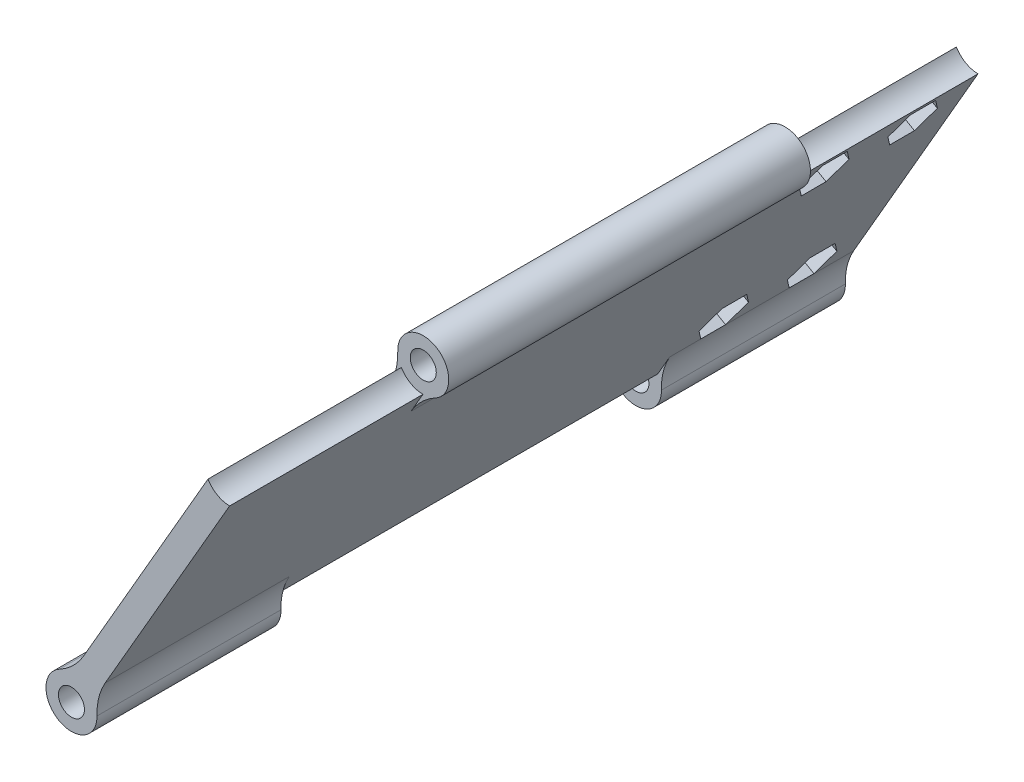
SolidWorks part; units mm, degrees
ref_plane "Front Plane" through (0, 0, 0) normal (0, 0, 1) x (1, 0, 0)
ref_plane "Top Plane" through (0, 0, 0) normal (0, 1, 0) x (1, 0, 0)
ref_plane "Right Plane" through (0, 0, 0) normal (1, 0, 0) x (0, 0, -1)
sketch "Sketch2" plane through (0, 0, 0) normal (0, 0, 1) x (1, 0, 0)
  line L0 (0, 0) -> (38.1, 0)
  line L1 (0, 0) -> (0, -38.1)
  circle A0 centre (0, 0) radius 38.1
  circle A1 centre (0, -29.337) radius 1.5875
  circle A2 centre (-25.4066, 14.6685) radius 1.5875
  circle A3 centre (25.4066, 14.6685) radius 1.5875
  point P13 (0, 0)
  dimension "D1" = 76.2
  dimension "D2" = 3.175
  dimension "D3" = 8.763
  dimension "D4" = 3
extrude "Boss-Extrude1" add sketch "Sketch2" along normal blind 10 contours A1 L1 L0 A0 A3 A2 | A1 L1 A0 L0
sketch "Sketch3" plane through (0, 0, 10) normal (0, 0, 1) x (1, 0, 0)
  line L1 (0, -29.337) -> (25.4066, 14.6685)
  line L2 (1.7321, -30.337) -> (27.1386, 13.6685)
  line L3 (-1.7321, -28.337) -> (23.6745, 15.6685)
  circle A11 centre (0, -29.337) radius 1.5875
  circle A12 centre (25.4066, 14.6685) radius 1.5875
  circle A17 centre (0, -29.337) radius 2.0875
  circle A18 centre (25.4066, 14.6685) radius 2.0875
  circle A19 centre (0, -29.337) radius 4.0875
  circle A20 centre (25.4066, 14.6685) radius 4.0875
  dimension "D1" = 0.5
  dimension "D2" = 2
  dimension "D4" = 2
  dimension "D5" = 2
extrude "Boss-Extrude2" add sketch "Sketch3" along normal blind 120 separate body contours L2 A20 L3 A18 | L1 A20 L2 A18 | L3 A20 L1 A18 | A20 L1 A19 L2 | A20 L3 A19 L1 | L1 A19 L3 A17 | L2 A19 L1 A17 | L3 A19 L2 A17
delete or keep bodies "Body-Delete/Keep 2" type delete bodies bodies 101
ref_plane "Plane1" through (0, 0, 70) normal (0, 0, 1) x (1, 0, 0)
sketch "Sketch4" plane through (0, 0, 70) normal (0, 0, 1) x (1, 0, 0)
  circle A1 centre (0, -29.337) radius 4.0875
extrude "Cut-Extrude1" cut sketch "Sketch4" against normal blind 30.5 and the other way blind 30.5
sketch "Sketch5" plane through (0, 0, 10) normal (0, 0, -1) x (-1, 0, 0)
  circle A0 centre (-25.4066, 14.6685) radius 4.0875
extrude "Cut-Extrude2" cut sketch "Sketch5" against normal offset from surface (31 mm away) 1.5 up to face at (2.0875, -29.337, 39.5) offset beyond the face yes
sketch "Sketch6" plane through (0, 0, 130) normal (0, 0, 1) x (1, 0, 0)
  circle A0 centre (25.4066, 14.6685) radius 4.0875
extrude "Cut-Extrude3" cut sketch "Sketch6" against normal offset from surface (31 mm away) 1.5 contours A0 up to face at (2.0875, -29.337, 100.5) offset beyond the face yes
fillet "Fillet1" radius 10 6 edges at (21.8921, 12.5813, 70) (0.0503, -25.2498, 24.75) (0.0503, -25.2498, 115.25) (3.5144, -27.2498, 115.25) (3.5144, -27.2498, 24.75) (25.3562, 10.5813, 70)
sketch "Sketch7" plane through (10.9712, -6.3343, 0) normal (-0.866, 0.5, 0) x (0, 0, 1)
  circle A0 centre (18.3842, -14.5821) radius 1.5
  circle A1 centre (32.5542, -14.5821) radius 1.5
  circle A2 centre (18.3842, 17.6479) radius 1.5
  circle A3 centre (32.5542, 17.6479) radius 1.5
extrude "Cut-Extrude4" cut sketch "Sketch7" against normal up to surface (4 mm away) contours A0 | A2 | A3 | A1 up to face at (14.7532, -7.7836, 70)
sketch "Sketch8" plane through (14.4353, -8.3343, 0) normal (0.866, -0.5, 0) x (0, 0, -1)
  line L25 (-28.5948, 17.6686) -> (-30.5924, 21.0872)
  line L26 (-30.5924, 21.0872) -> (-34.5518, 21.0665)
  line L27 (-34.5518, 21.0665) -> (-36.5137, 17.6272)
  line L28 (-36.5137, 17.6272) -> (-34.5161, 14.2086)
  line L29 (-34.5161, 14.2086) -> (-30.5566, 14.2293)
  line L30 (-30.5566, 14.2293) -> (-28.5948, 17.6686)
  line L31 (-14.4248, 17.6686) -> (-16.4224, 21.0872)
  line L32 (-16.4224, 21.0872) -> (-20.3818, 21.0665)
  line L33 (-20.3818, 21.0665) -> (-22.3437, 17.6272)
  line L34 (-22.3437, 17.6272) -> (-20.3461, 14.2086)
  line L35 (-20.3461, 14.2086) -> (-16.3866, 14.2293)
  line L36 (-16.3866, 14.2293) -> (-14.4248, 17.6686)
  line L37 (-14.4248, -14.5614) -> (-16.4224, -11.1428)
  line L38 (-16.4224, -11.1428) -> (-20.3818, -11.1635)
  line L39 (-20.3818, -11.1635) -> (-22.3437, -14.6028)
  line L40 (-22.3437, -14.6028) -> (-20.3461, -18.0214)
  line L41 (-20.3461, -18.0214) -> (-16.3866, -18.0007)
  line L42 (-16.3866, -18.0007) -> (-14.4248, -14.5614)
  line L43 (-28.5948, -14.5614) -> (-30.5924, -11.1428)
  line L44 (-30.5924, -11.1428) -> (-34.5518, -11.1635)
  line L45 (-34.5518, -11.1635) -> (-36.5137, -14.6028)
  line L46 (-36.5137, -14.6028) -> (-34.5161, -18.0214)
  line L47 (-34.5161, -18.0214) -> (-30.5566, -18.0007)
  line L48 (-30.5566, -18.0007) -> (-28.5948, -14.5614)
  circle A0 centre (-32.5542, 17.6479) radius 3.429 construction
  circle A1 centre (-18.3842, 17.6479) radius 3.429 construction
  circle A2 centre (-18.3842, -14.5821) radius 3.429 construction
  circle A3 centre (-32.5542, -14.5821) radius 3.429 construction
  circle M4 centre (-32.5542, 17.6479) radius 1.5
  circle M5 centre (-18.3842, 17.6479) radius 1.5
  circle M6 centre (-18.3842, -14.5821) radius 1.5
  dimension "D1" = 6.858
extrude "Cut-Extrude5" cut sketch "Sketch8" against normal blind 2 contours L29 L30 L25 L26 L27 L28 M6 | L47 L48 L43 L44 L45 L46 M5 | L41 L42 L37 L38 L39 L40 M4 | L35 L36 L31 L32 L33 L34
